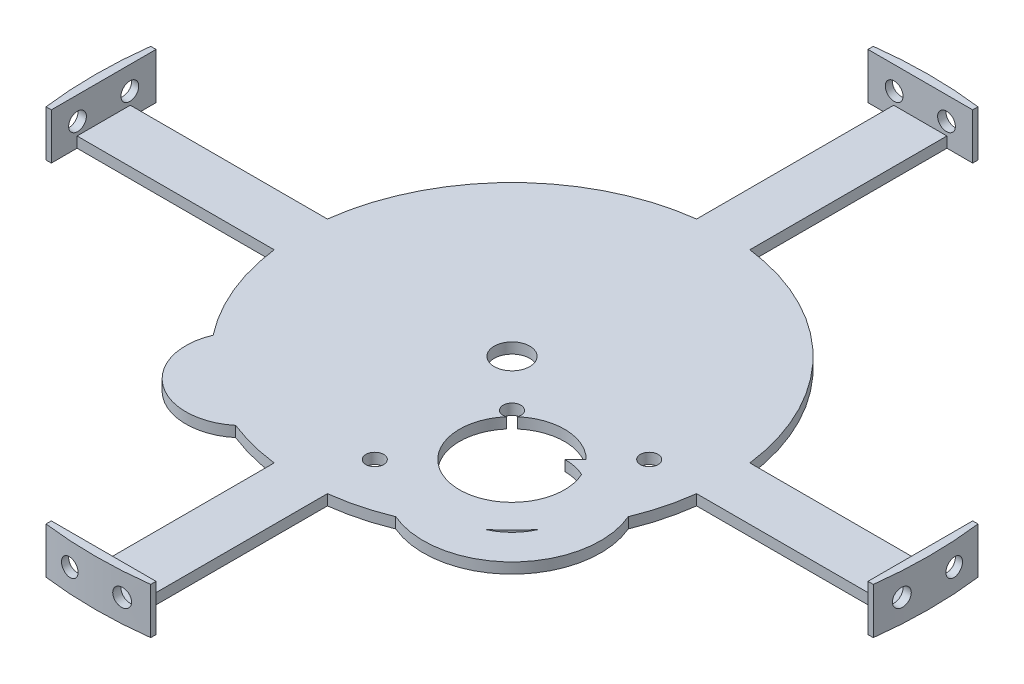
SolidWorks part; units mm, degrees
material "1060 Alloy"
ref_plane "Front Plane" through (0, 0, 0) normal (0, 0, 1) x (1, 0, 0)
ref_plane "Top Plane" through (0, 0, 0) normal (0, 1, 0) x (1, 0, 0)
ref_plane "Right Plane" through (0, 0, 0) normal (1, 0, 0) x (0, 0, -1)
sketch "Sketch1" plane through (0, 0, 0) normal (0, 1, 0) x (1, 0, 0)
  circle A0 centre (0, 0) radius 76.2
  dimension "D1" = 152.4
extrude "Boss-Extrude1" add sketch "Sketch1" along normal blind 3.81 contours A0
sketch "Sketch3" plane through (0, 0, 0) normal (0, -1, 0) x (-1, 0, 0)
  line L0 (9.525, -9.525) -> (148.9207, -9.525)
  line L3 (9.525, 9.525) -> (148.9207, 9.525)
  line L6 (-9.525, -9.525) -> (-9.525, -148.9207)
  line L7 (9.525, -9.525) -> (9.525, -148.9207)
  line L9 (-9.525, 9.525) -> (-148.9207, 9.525)
  line L10 (-9.525, -9.525) -> (-148.9207, -9.525)
  line L12 (9.525, 9.525) -> (9.525, 148.9207)
  line L13 (-9.525, 9.525) -> (-9.525, 148.9207)
  line L14 (0, 0) -> (149.225, 0) construction
  line L15 (13.694, 9.525) -> (13.694, -9.525) construction
  line L16 (0, 149.225) -> (0, -149.225) construction
  arc A0 (148.9207, -9.525) -> (148.9207, 9.525) centre (0, 0) ccw
  arc A1 (-9.525, -148.9207) -> (9.525, -148.9207) centre (0, 0) ccw
  arc A2 (-148.9207, 9.525) -> (-148.9207, -9.525) centre (0, 0) ccw
  arc A3 (9.525, 148.9207) -> (-9.525, 148.9207) centre (0, 0) ccw
  point P22 (0, 0)
  dimension "D2" = 19.05
  dimension "D3" = 298.45
  dimension "D1" = 4
extrude "Boss-Extrude3" add sketch "Sketch3" against normal blind 3.81
sketch "Sketch5" plane through (0, 3.81, 0) normal (0, 1, 0) x (1, 0, 0)
  circle A1 centre (0, 0) radius 6.35
  dimension "D1" = 12.7
extrude "Cut-Extrude1" cut sketch "Sketch5" against normal through all
sketch "Sketch7" plane through (0, 3.81, 0) normal (0, 1, 0) x (1, 0, 0)
  line L0 (0, 149.225) -> (0, 0) construction
  line L2 (18.7397, 148.0437) -> (18.7397, 146.1387)
  line L3 (18.7397, 146.1387) -> (-18.7397, 146.1387)
  line L4 (-18.7397, 148.0437) -> (-18.7397, 146.1387)
  arc A0 (18.7397, 148.0437) -> (-18.7397, 148.0437) centre (0, 0) ccw
  dimension "D1" = 149.225
extrude "Boss-Extrude4" add sketch "Sketch7" along normal blind 12.7 and the other way blind 3.81
sketch "Sketch8" plane through (0, 0, -146.1387) normal (0, 0, 1) x (1, 0, 0)
  line L0 (0, 16.51) -> (0, 0) construction
  line L3 (18.7397, 16.51) -> (-18.7397, 16.51) construction
  line L5 (-18.7397, 0) -> (18.7397, 0) construction
  line L6 (0, 8.255) -> (-18.7397, 8.255) construction
  line L7 (-18.7397, 0) -> (-18.7397, 16.51) construction
  circle A4 centre (-9.3699, 8.255) radius 3.175
  circle A5 centre (9.3699, 8.255) radius 3.175
  dimension "D1" = 6.35
extrude "Cut-Extrude3" cut sketch "Sketch8" against normal through all
pattern_circular "CirPattern3" count 4 over 360 about axis through (0, 0, 0) along (0, 1, 0) of "Cut-Extrude3", "Boss-Extrude4"
sketch "Sketch9" plane through (0, 0, 0) normal (0, -1, 0) x (1, 0, 0)
  circle A0 centre (-56.515, -23.8125) radius 3.175
  circle A1 centre (-15.875, -23.8125) radius 3.175
extrude "Cut-Extrude4" cut sketch "Sketch9" against normal up to surface (3.81 mm away)
sketch "Sketch10" plane through (0, 3.81, 0) normal (0, 1, 0) x (1, 0, 0)
sketch "Sketch11" plane through (0, 3.81, 0) normal (0, 1, 0) x (1, 0, 0)
  circle A0 centre (41.275, -41.275) radius 25.4
  circle A1 centre (41.275, -41.275) radius 31.75
extrude "Boss-Extrude5" add sketch "Sketch11" against normal blind 3.81
sketch "Sketch12" plane through (0, 3.81, 0) normal (0, 1, 0) x (1, 0, 0)
  circle A0 centre (41.275, -41.275) radius 25.4
extrude "Cut-Extrude5" cut sketch "Sketch12" against normal blind 3.81
sketch "Sketch13" plane through (0, 3.81, 0) normal (0, 1, 0) x (1, 0, 0)
  circle A0 centre (-41.1687, -55.0334) radius 20.5295
  circle A1 centre (-41.1711, -70.7309) radius 2.3622
  circle A2 centre (-41.1663, -39.3359) radius 2.3622
extrude "Boss-Extrude7" add sketch "Sketch13" against normal blind 3.81
sketch "Sketch14" plane through (0, 3.81, 0) normal (0, 1, 0) x (1, 0, 0)
  circle A0 centre (-41.1663, -39.3359) radius 2.3622
extrude "Cut-Extrude6" cut sketch "Sketch14" against normal blind 3.81
sketch "Sketch15" plane through (0, 3.81, 0) normal (0, 1, 0) x (1, 0, 0)
  circle A0 centre (16.7207, -16.7207) radius 3.175
  circle A1 centre (65.8293, -16.7207) radius 3.175
  circle A2 centre (16.7207, -65.8293) radius 3.175
extrude "Cut-Extrude7" cut sketch "Sketch15" against normal blind 3.81
sketch "Sketch16" plane through (0, 3.81, 0) normal (0, 1, 0) x (1, 0, 0)
  line L12 (-9.525, -75.6023) -> (-9.525, -146.1387)
  line L13 (-9.525, -146.1387) -> (9.525, -146.1387)
  line L14 (9.525, -146.1387) -> (9.525, -75.6023)
  line L15 (75.6023, -9.525) -> (146.1387, -9.525)
  line L16 (146.1387, -9.525) -> (146.1387, 9.525)
  line L17 (146.1387, 9.525) -> (75.6023, 9.525)
  line L18 (9.525, 75.6023) -> (9.525, 146.1387)
  line L19 (9.525, 146.1387) -> (-9.525, 146.1387)
  line L20 (-9.525, 146.1387) -> (-9.525, 75.6023)
  line L21 (-75.6023, 9.525) -> (-146.1387, 9.525)
  line L22 (-146.1387, 9.525) -> (-146.1387, -9.525)
  line L23 (-146.1387, -9.525) -> (-75.6023, -9.525)
  line L24 (-9.525, -75.6023) -> (-9.525, -146.1387)
  line L25 (-9.525, -146.1387) -> (9.525, -146.1387)
  line L26 (9.525, -146.1387) -> (9.525, -75.6023)
  line L27 (75.6023, -9.525) -> (146.1387, -9.525)
  line L28 (146.1387, -9.525) -> (146.1387, 9.525)
  line L29 (146.1387, 9.525) -> (75.6023, 9.525)
  line L30 (9.525, 75.6023) -> (9.525, 146.1387)
  line L31 (9.525, 146.1387) -> (-9.525, 146.1387)
  line L32 (-9.525, 146.1387) -> (-9.525, 75.6023)
  line L33 (-75.6023, 9.525) -> (-146.1387, 9.525)
  line L34 (-146.1387, 9.525) -> (-146.1387, -9.525)
  line L35 (-146.1387, -9.525) -> (-75.6023, -9.525)
  circle A0 centre (41.275, -41.275) radius 18.796
  circle A1 centre (41.275, -41.275) radius 25.4
  arc A8 (-75.6023, -9.525) -> (-60.0321, -46.9318) centre (0, 0) ccw
  arc A9 (-60.0321, -46.9318) -> (-28.0702, -70.8414) centre (-41.1687, -55.0334) ccw
  arc A10 (-28.0702, -70.8414) -> (-9.525, -75.6023) centre (0, 0) ccw
  arc A11 (9.525, -75.6023) -> (28.8915, -70.5104) centre (0, 0) ccw
  arc A12 (28.8915, -70.5104) -> (70.5104, -28.8915) centre (41.275, -41.275) ccw
  arc A13 (70.5104, -28.8915) -> (75.6023, -9.525) centre (0, 0) ccw
  arc A14 (75.6023, 9.525) -> (9.525, 75.6023) centre (0, 0) ccw
  arc A15 (-9.525, 75.6023) -> (-75.6023, 9.525) centre (0, 0) ccw
  arc A16 (-75.6023, -9.525) -> (-60.0321, -46.9318) centre (0, 0) ccw
  arc A17 (-60.0321, -46.9318) -> (-28.0702, -70.8414) centre (-41.1687, -55.0334) ccw
  arc A18 (-28.0702, -70.8414) -> (-9.525, -75.6023) centre (0, 0) ccw
  arc A19 (9.525, -75.6023) -> (28.8915, -70.5104) centre (0, 0) ccw
  arc A20 (28.8915, -70.5104) -> (70.5104, -28.8915) centre (41.275, -41.275) ccw
  arc A21 (70.5104, -28.8915) -> (75.6023, -9.525) centre (0, 0) ccw
  arc A22 (75.6023, 9.525) -> (9.525, 75.6023) centre (0, 0) ccw
  arc A23 (-9.525, 75.6023) -> (-75.6023, 9.525) centre (0, 0) ccw
  circle M45 centre (41.275, -41.275) radius 25.4
  dimension "D2" = 37.592
  dimension "D1" = 0
extrude "Boss-Extrude8" add sketch "Sketch16" against normal up to surface (3.81 mm away) contours A0 M45 up to face at (16.7207, 0, 69.0043)
sketch "Sketch17" plane through (0, 3.81, 0) normal (0, 1, 0) x (1, 0, 0)
  line L0 (0, 0) -> (41.275, -41.275)
  line L1 (0, 0) -> (10.0579, -10.0579)
  line L2 (0, 0) -> (53.8815, -53.8815)
  line L3 (10.0579, -10.0579) -> (53.8815, -53.8815)
  line L4 (53.8815, -53.8815) -> (10.0579, -10.0579)
  line L5 (31.9697, -31.9697) -> (52.0193, -11.9201)
  line L12 (-9.525, -75.6023) -> (-9.525, -146.1387)
  line L13 (-9.525, -146.1387) -> (9.525, -146.1387)
  line L14 (9.525, -146.1387) -> (9.525, -75.6023)
  line L15 (75.6023, -9.525) -> (146.1387, -9.525)
  line L16 (146.1387, -9.525) -> (146.1387, 9.525)
  line L17 (146.1387, 9.525) -> (75.6023, 9.525)
  line L18 (9.525, 75.6023) -> (9.525, 146.1387)
  line L19 (9.525, 146.1387) -> (-9.525, 146.1387)
  line L20 (-9.525, 146.1387) -> (-9.525, 75.6023)
  line L21 (-75.6023, 9.525) -> (-146.1387, 9.525)
  line L22 (-146.1387, 9.525) -> (-146.1387, -9.525)
  line L23 (-146.1387, -9.525) -> (-75.6023, -9.525)
  line L24 (-9.525, -75.6023) -> (-9.525, -146.1387)
  line L25 (-9.525, -146.1387) -> (9.525, -146.1387)
  line L26 (9.525, -146.1387) -> (9.525, -75.6023)
  line L27 (75.6023, -9.525) -> (146.1387, -9.525)
  line L28 (146.1387, -9.525) -> (146.1387, 9.525)
  line L29 (146.1387, 9.525) -> (75.6023, 9.525)
  line L30 (9.525, 75.6023) -> (9.525, 146.1387)
  line L31 (9.525, 146.1387) -> (-9.525, 146.1387)
  line L32 (-9.525, 146.1387) -> (-9.525, 75.6023)
  line L33 (-75.6023, 9.525) -> (-146.1387, 9.525)
  line L34 (-146.1387, 9.525) -> (-146.1387, -9.525)
  line L35 (-146.1387, -9.525) -> (-75.6023, -9.525)
  circle A1 centre (41.275, -41.275) radius 18.796
  circle A2 centre (65.8293, -16.7207) radius 3.175
  circle A3 centre (16.7207, -65.8293) radius 3.175
  circle A4 centre (0, 0) radius 76.2
  circle A5 centre (0, 0) radius 14.224
  circle A6 centre (31.9697, -31.9697) radius 18.796
  circle A7 centre (56.524, -7.4154) radius 3.175
  arc A8 (-75.6023, -9.525) -> (-60.0321, -46.9318) centre (0, 0) ccw
  arc A9 (-60.0321, -46.9318) -> (-28.0702, -70.8414) centre (-41.1687, -55.0334) ccw
  arc A10 (-28.0702, -70.8414) -> (-9.525, -75.6023) centre (0, 0) ccw
  arc A11 (9.525, -75.6023) -> (28.8915, -70.5104) centre (0, 0) ccw
  arc A12 (28.8915, -70.5104) -> (70.5104, -28.8915) centre (41.275, -41.275) ccw
  arc A13 (70.5104, -28.8915) -> (75.6023, -9.525) centre (0, 0) ccw
  arc A14 (75.6023, 9.525) -> (9.525, 75.6023) centre (0, 0) ccw
  arc A15 (-9.525, 75.6023) -> (-75.6023, 9.525) centre (0, 0) ccw
  arc A16 (-75.6023, -9.525) -> (-60.0321, -46.9318) centre (0, 0) ccw
  arc A17 (-60.0321, -46.9318) -> (-28.0702, -70.8414) centre (-41.1687, -55.0334) ccw
  arc A18 (-28.0702, -70.8414) -> (-9.525, -75.6023) centre (0, 0) ccw
  arc A19 (9.525, -75.6023) -> (28.8915, -70.5104) centre (0, 0) ccw
  arc A20 (28.8915, -70.5104) -> (70.5104, -28.8915) centre (41.275, -41.275) ccw
  arc A21 (70.5104, -28.8915) -> (75.6023, -9.525) centre (0, 0) ccw
  arc A22 (75.6023, 9.525) -> (9.525, 75.6023) centre (0, 0) ccw
  arc A23 (-9.525, 75.6023) -> (-75.6023, 9.525) centre (0, 0) ccw
  circle A24 centre (7.4154, -56.524) radius 3.175
  circle M25 centre (16.7207, -16.7207) radius 3.175
  circle M51 centre (41.275, -41.275) radius 18.796
  dimension "D2" = 28.448
  dimension "D3" = 14.224
  dimension "D1" = 0
extrude "Cut-Extrude8" cut sketch "Sketch17" against normal through all contours A6 A1 L0 M25 | L5 A6 L0 M25 M51 | A7 | A24
sketch "Sketch19" plane through (0, 3.81, 0) normal (0, 1, 0) x (1, 0, 0)
  line L0 (0, 0) -> (41.275, -41.275)
  line L1 (0, 0) -> (10.0579, -10.0579)
  line L2 (0, 0) -> (53.8815, -53.8815)
  line L3 (10.0579, -10.0579) -> (53.8815, -53.8815)
  line L4 (53.8815, -53.8815) -> (10.0579, -10.0579)
  line L5 (31.9697, -31.9697) -> (52.0193, -11.9201)
  line L6 (-9.525, -75.6023) -> (-9.525, -142.9888)
  line L7 (-9.525, -142.9888) -> (9.525, -142.9888)
  line L8 (9.525, -142.9888) -> (9.525, -75.6023)
  line L9 (75.6023, -9.525) -> (142.9888, -9.525)
  line L10 (142.9888, -9.525) -> (142.9888, 9.525)
  line L11 (142.9888, 9.525) -> (75.6023, 9.525)
  line L12 (9.525, 75.6023) -> (9.525, 142.9888)
  line L13 (9.525, 142.9888) -> (-9.525, 142.9888)
  line L14 (-9.525, 142.9888) -> (-9.525, 75.6023)
  line L15 (-75.6023, 9.525) -> (-142.9888, 9.525)
  line L16 (-142.9888, 9.525) -> (-142.9888, -9.525)
  line L17 (-142.9888, -9.525) -> (-75.6023, -9.525)
  circle A0 centre (41.275, -41.275) radius 18.796
  circle A1 centre (65.8293, -16.7207) radius 3.175
  circle A2 centre (16.7207, -65.8293) radius 3.175
  circle A3 centre (0, 0) radius 76.2
  circle A4 centre (0, 0) radius 14.224
  circle A5 centre (31.9697, -31.9697) radius 18.796
  circle A6 centre (56.524, -7.4154) radius 3.175
  arc A7 (-75.6023, -9.525) -> (-60.0321, -46.9318) centre (0, 0) ccw
  arc A8 (-60.0321, -46.9318) -> (-28.0702, -70.8414) centre (-41.1687, -55.0334) ccw
  arc A9 (-28.0702, -70.8414) -> (-9.525, -75.6023) centre (0, 0) ccw
  arc A10 (9.525, -75.6023) -> (28.8915, -70.5104) centre (0, 0) ccw
  arc A11 (28.8915, -70.5104) -> (70.5104, -28.8915) centre (41.275, -41.275) ccw
  arc A12 (70.5104, -28.8915) -> (75.6023, -9.525) centre (0, 0) ccw
  arc A13 (75.6023, 9.525) -> (9.525, 75.6023) centre (0, 0) ccw
  arc A14 (-9.525, 75.6023) -> (-75.6023, 9.525) centre (0, 0) ccw
  circle A15 centre (7.4154, -56.524) radius 3.175
  dimension "D1" = 28.448
  dimension "D2" = 14.224
extrude "Boss-Extrude9" add sketch "Sketch19" against normal up to surface (3.81 mm away)
equation "\"BoltClearance\"= .25"
equation "\"Actuator_Plate\"=6"
equation "\"Rocket Diameter\"= 12"
equation "\"D3@Sketch3\"= \"Rocket Diameter\" - .25"
equation "\"D1@Sketch8\"=\"BoltClearance\""
